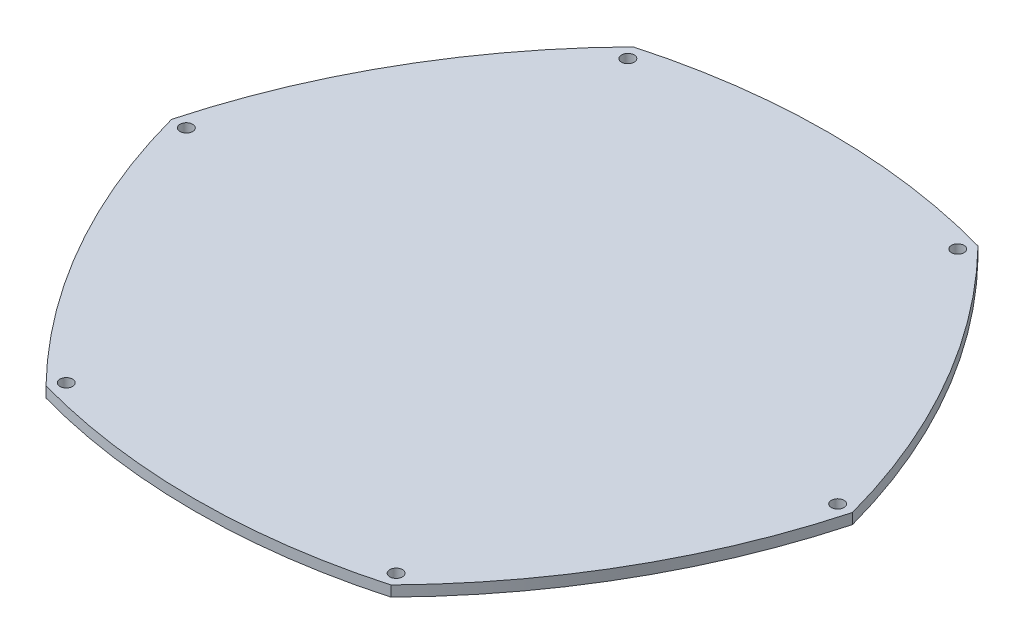
SolidWorks part; units mm, degrees
material "6061 Alloy"
ref_plane "Front Plane" through (0, 0, 0) normal (0, 0, 1) x (1, 0, 0)
ref_plane "Top Plane" through (0, 0, 0) normal (0, 1, 0) x (1, 0, 0)
ref_plane "Right Plane" through (0, 0, 0) normal (1, 0, 0) x (0, 0, -1)
sketch "Sketch1" plane through (0, 0, 0) normal (0, 1, 0) x (1, 0, 0)
  line L0 (-39, -66.3928) -> (39, -66.3928) construction
  line L1 (0, 0) -> (0, -66.3928) construction
  line L2 (0, 0) -> (-40.7727, -69.4106) construction
  line L3 (0, 0) -> (40.7727, -69.4106) construction
  line L4 (0, 0) -> (-77, 0) construction
  line L5 (0, 0) -> (77, 0) construction
  line L6 (0, 0) -> (-80.5, 0) construction
  line L7 (0, 0) -> (80.5, 0) construction
  line L8 (0, 0) -> (40.7727, 69.4106) construction
  line L9 (0, 0) -> (-40.7727, 69.4106) construction
  circle A1 centre (-39, -66.3928) radius 1.5
  circle A2 centre (39, -66.3928) radius 1.5
  circle A3 centre (0, 0) radius 73.5
  circle A4 centre (0, 0) radius 75
  arc A5 (-40.7727, -69.4106) -> (40.7727, -69.4106) centre (0, 76.5068) ccw
  circle A6 centre (-77, 0) radius 1.5
  circle A7 centre (77, 0) radius 1.5
  arc A8 (-80.5, 0) -> (-40.7727, -69.4106) centre (72.2865, 41.3733) ccw
  arc A9 (40.7727, -69.4106) -> (80.5, 0) centre (-72.2865, 41.3733) ccw
  circle A10 centre (39, 66.3928) radius 1.5
  circle A11 centre (-39, 66.3928) radius 1.5
  arc A12 (-80.5, 0) -> (-40.7727, 69.4106) centre (72.2865, -41.3733) cw
  arc A13 (-40.7727, 69.4106) -> (40.7727, 69.4106) centre (0, -76.5068) cw
  arc A14 (40.7727, 69.4106) -> (80.5, 0) centre (-72.2865, -41.3733) cw
  dimension "D2" = 3
  dimension "D3" = 3
  dimension "D4" = 78
  dimension "D6" = 147
  dimension "D7" = 150
  dimension "D8" = 3
  dimension "D9" = 3
  dimension "D5" = 80.5
  dimension "D10" = 77
  dimension "D11" = 77
  dimension "D12" = 80.5
  dimension "D13" = 80.5
  dimension "D14" = 80.5
  dimension "D15" = 3.5
extrude "Boss-Extrude1" add sketch "Sketch1" along normal blind 2.5 contours A3 | A4 A3 | A12 A8 A4 A6 | A4 A8 A5 A1 | A5 A9 A4 A2 | A14 A4 A9 A7 | A14 A13 A4 A10 | A13 A12 A4 A11
